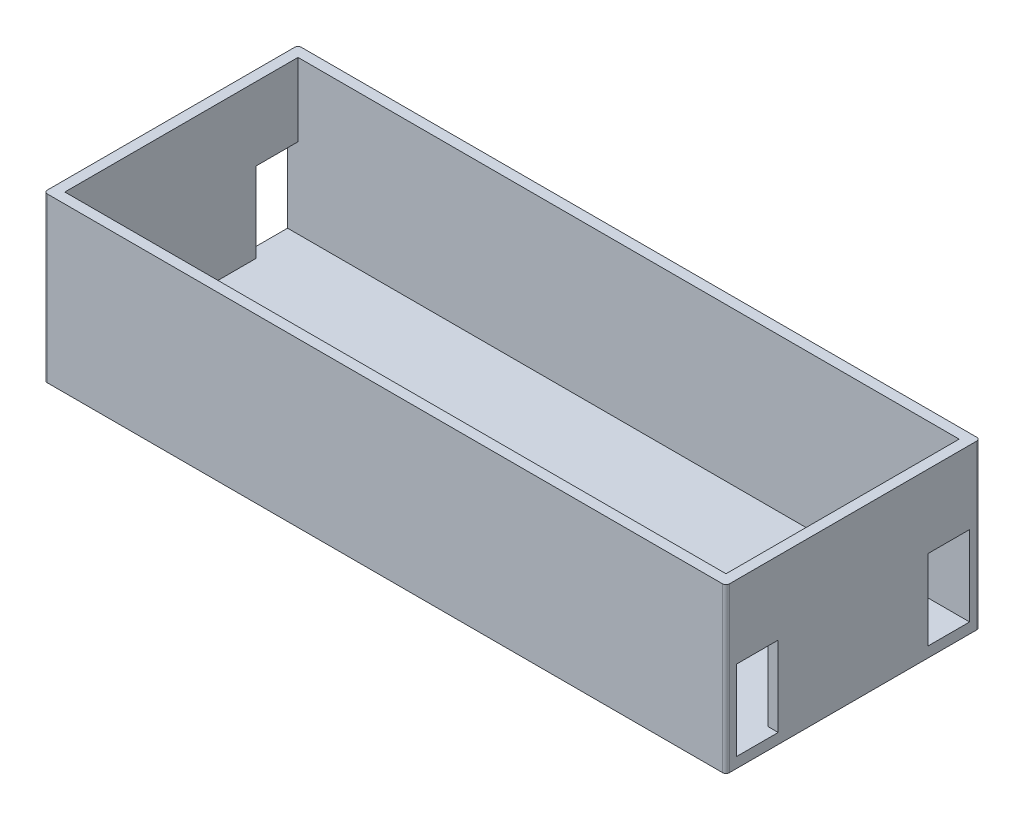
SolidWorks part; units mm, degrees
ref_plane "Front Plane" through (0, 0, 0) normal (0, 0, 1) x (1, 0, 0)
ref_plane "Top Plane" through (0, 0, 0) normal (0, 1, 0) x (1, 0, 0)
ref_plane "Right Plane" through (0, 0, 0) normal (1, 0, 0) x (0, 0, -1)
sketch "Sketch1" plane through (0, 0, 0) normal (0, 1, 0) x (1, 0, 0)
  line L1 (0, 0) -> (196, 0)
  line L2 (0, 0) -> (0, 73)
  line L3 (0, 73) -> (196, 73)
  line L4 (196, 0) -> (196, 73)
  dimension "D1" = 73
  dimension "D2" = 196
extrude "Boss-Extrude1" add sketch "Sketch1" along normal blind 3
sketch "Sketch3" plane through (0, 3, 0) normal (0, 1, 0) x (1, 0, 0)
  line L1 (3, 70) -> (193, 70)
  line L2 (3, 70) -> (3, 3)
  line L3 (3, 3) -> (193, 3)
  line L4 (0, 0) -> (196, 0)
  line L5 (196, 0) -> (196, 73)
  line L6 (196, 73) -> (0, 73)
  line L7 (0, 73) -> (0, 0)
  line L8 (0, 0) -> (196, 0)
  line L9 (196, 0) -> (196, 73)
  line L10 (196, 73) -> (0, 73)
  line L11 (0, 73) -> (0, 0)
  line L12 (193, 70) -> (193, 3)
  dimension "D2" = 3
  dimension "D3" = 3
  dimension "D4" = 3
  dimension "D5" = 3
  dimension "D1" = 0
extrude "Boss-Extrude2" add sketch "Sketch3" along normal blind 44
fillet "Fillet1" radius 1 4 edges at (0, 23.5, -73) (0, 23.5, 0) (196, 23.5, -73) (196, 23.5, 0)
sketch "Sketch4" plane through (196, 0, 0) normal (1, 0, 0) x (0, 0, -1)
  line L0 (0, 0) -> (0, 47) construction
  line L1 (3, 26) -> (15, 26)
  line L2 (3, 26) -> (3, 3)
  line L3 (3, 3) -> (15, 3)
  line L4 (15, 26) -> (15, 3)
  line L5 (1, 0) -> (72, 0) construction
  line L6 (73, 47) -> (73, 0) construction
  line L7 (58, 26) -> (70, 26)
  line L8 (58, 26) -> (58, 3)
  line L9 (58, 3) -> (70, 3)
  line L10 (70, 26) -> (70, 3)
  dimension "D1" = 3
  dimension "D2" = 3
  dimension "D3" = 12
  dimension "D4" = 23
  dimension "D5" = 3
  dimension "D6" = 3
extrude "Cut-Extrude1" cut sketch "Sketch4" against normal through all
